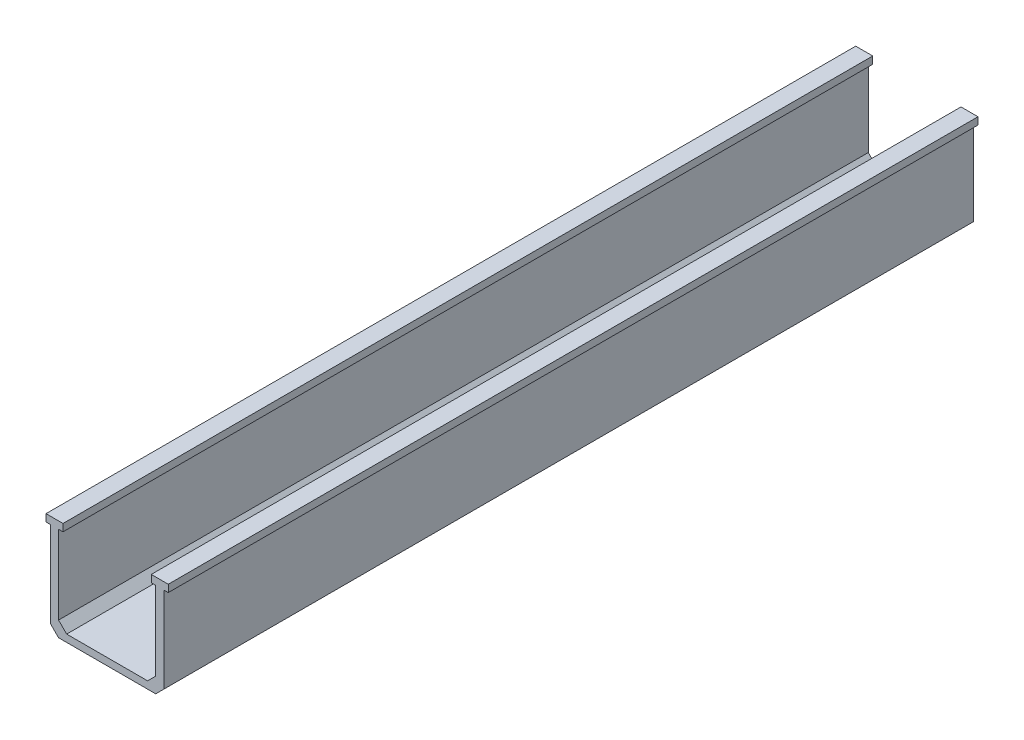
SolidWorks part; units mm, degrees
ref_plane "Plan de face" through (0, 0, 0) normal (0, 0, 1) x (1, 0, 0)
ref_plane "Plan de dessus" through (0, 0, 0) normal (0, 1, 0) x (1, 0, 0)
ref_plane "Plan de droite" through (0, 0, 0) normal (1, 0, 0) x (0, 0, -1)
sketch "Esquisse1" plane through (0, 0, 0) normal (0, 0, 1) x (1, 0, 0)
  line L1 (-14, -12.5) -> (14, -12.5)
  line L2 (-14, -12.5) -> (-14, 10.7143)
  line L3 (-14, 12.5) -> (-10.8998, 12.5)
  line L4 (14, -12.5) -> (14, 10.7143)
  line L5 (-14, -12.5) -> (14, 12.5) construction
  line L6 (-14, 12.5) -> (14, -12.5) construction
  line L7 (-12, -10.7143) -> (12, -10.7143)
  line L8 (-12, -10.7143) -> (-12, 10.7143)
  line L9 (-12, 10.7143) -> (-10.8998, 10.7143)
  line L10 (12, -10.7143) -> (12, 10.7143)
  line L11 (-12, -10.7143) -> (12, 10.7143) construction
  line L12 (-12, 10.7143) -> (12, -10.7143) construction
  line L14 (-13, 10.7143) -> (-13, 12.5) construction
  line L15 (14, 10.7143) -> (15.1002, 10.7143)
  line L16 (-10.8998, 10.7143) -> (-12, 10.7143)
  line L17 (-10.8998, 10.7143) -> (-10.8998, 12.5)
  line L18 (-10.8998, 12.5) -> (-15.1002, 12.5)
  line L19 (-15.1002, 10.7143) -> (-15.1002, 12.5)
  line L20 (-10.8998, 10.7143) -> (-15.1002, 12.5) construction
  line L21 (-10.8998, 12.5) -> (-15.1002, 10.7143) construction
  line L22 (10.8998, 10.7143) -> (12, 10.7143)
  line L23 (10.8998, 10.7143) -> (10.8998, 12.5)
  line L24 (10.8998, 12.5) -> (15.1002, 12.5)
  line L25 (15.1002, 10.7143) -> (15.1002, 12.5)
  line L26 (10.8998, 12.5) -> (14, 12.5)
  line L27 (10.8998, 10.7143) -> (12, 10.7143)
  line L28 (-14, 10.7143) -> (-15.1002, 10.7143)
  point P0 (0, 0)
  point P6 (0, 0)
  point P14 (-13, 11.6071)
  dimension "D1" = 28
  dimension "D2" = 25
  dimension "D3" = 24
extrude "Boss.-Extru.1" add sketch "Esquisse1" along normal blind 200 contours L28 L2 L1 L4 L15 L25 L24 L23 L22 L10 L7 L8 L9 L17 L3 L18 L19
chamfer "Chanfrein1" distance 2 angle 45 2 edges at (-14, -12.5, 100) (14, -12.5, 100)
sketch "Esquisse2" plane through (0, -12.5, 0) normal (0, -1, 0) x (1, 0, 0)
  line L0 (0, 200) -> (0, 0) construction
  line L1 (-12, 200) -> (12, 200) construction
  line L2 (0, 0) -> (0, 100) construction
  line L3 (0, 100) -> (26.9869, 100) construction
  line L4 (0, 100) -> (0, 175.0004) construction
  circle A0 centre (0, 100) radius 3
  circle A1 centre (0, 175.0004) radius 3
  circle A2 centre (0, 24.9996) radius 3
extrude "Enlèv. mat.-Extru.1" cut sketch "Esquisse2" against normal through all both and the other way through all
chamfer "Chanfrein2" distance 2 angle 45 1 edges at (-12, -10.7143, 100)
chamfer "Chanfrein3" distance 2 angle 45 1 edges at (12, -10.7143, 100)
sketch "Esquisse3" plane through (0, -12.5, 0) normal (0, 1, 0) x (1, 0, 0)
  line L0 (0, -80.2712) -> (0, -99.3579) construction
  line L1 (-351.1273, -80.2712) -> (-2.9877, -80.2712) construction
  line L2 (-351.1273, -99.3579) -> (1648.8727, -99.3579) construction
